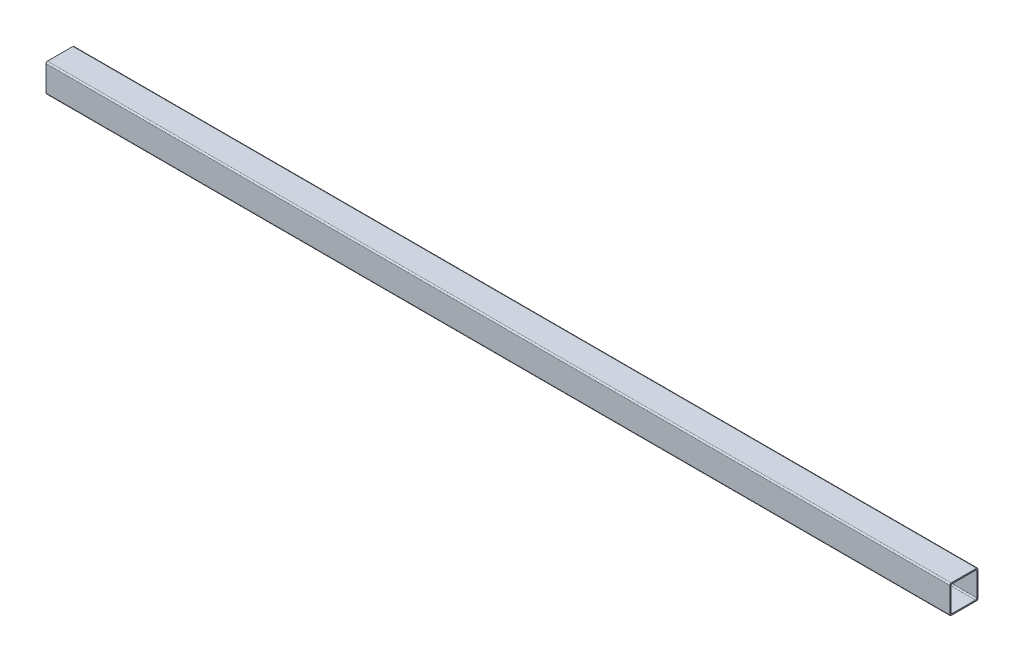
SolidWorks part; units mm, degrees
ref_plane "Front" through (0, 0, 0) normal (0, 0, 1) x (1, 0, 0)
ref_plane "Top" through (0, 0, 0) normal (0, 1, 0) x (1, 0, 0)
ref_plane "Right" through (0, 0, 0) normal (1, 0, 0) x (0, 0, -1)
sketch "Sketch1" plane through (0, 0, 0) normal (1, 0, 0) x (0, 0, -1)
  line L0 (-17.399, 0) -> (-19.05, 0) construction
  line L1 (17.145, -19.05) -> (-17.145, -19.05) construction
  line L2 (19.05, -17.145) -> (19.05, 17.145) construction
  line L3 (17.145, 19.05) -> (-17.145, 19.05) construction
  line L4 (-19.05, -17.145) -> (-19.05, 17.145) construction
  line L5 (19.05, -19.05) -> (-19.05, 19.05) construction
  line L6 (19.05, 19.05) -> (-19.05, -19.05) construction
  line L7 (15.6591, 17.399) -> (-15.6591, 17.399) construction
  line L8 (17.399, 15.6591) -> (17.399, -15.6591) construction
  line L9 (15.6591, -17.399) -> (-15.6591, -17.399) construction
  line L10 (-17.399, 15.6591) -> (-17.399, -15.6591) construction
  line L11 (17.399, 17.399) -> (-17.399, -17.399) construction
  line L12 (17.399, -17.399) -> (-17.399, 17.399) construction
  line L13 (0, -17.399) -> (0, -19.05) construction
  line L14 (17.399, -15.6591) -> (17.399, -19.05) construction
  line L15 (17.399, 0) -> (19.05, 0) construction
  line L16 (17.399, -19.05) -> (19.05, -19.05) construction
  arc A0 (-15.6591, -17.399) -> (-17.399, -15.6591) centre (-15.6591, -15.6591) cw construction
  arc A1 (17.399, -15.6591) -> (15.6591, -17.399) centre (15.6591, -15.6591) cw construction
  arc A2 (15.6591, 17.399) -> (17.399, 15.6591) centre (15.6591, 15.6591) cw construction
  arc A3 (-15.6591, 17.399) -> (-17.399, 15.6591) centre (-15.6591, 15.6591) ccw construction
  arc A4 (17.145, -19.05) -> (19.05, -17.145) centre (17.145, -17.145) ccw construction
  arc A5 (19.05, 17.145) -> (17.145, 19.05) centre (17.145, 17.145) ccw construction
  arc A6 (-17.145, 19.05) -> (-19.05, 17.145) centre (-17.145, 17.145) ccw construction
  arc A7 (-17.145, -19.05) -> (-19.05, -17.145) centre (-17.145, -17.145) cw construction
  point P0 (0, 0)
  point P6 (0, 0)
  dimension "D2" = 1.7399
  dimension "D3" = 1.905
  dimension "Outside Width" = 38.1
  dimension "Ouside Height" = 38.1
  dimension "Inside Height" = 34.798
  dimension "Wall Thickness" = 1.651
sketch "Sketch2" plane through (0, 0, 0) normal (0, 0, 1) x (1, 0, 0)
  line L0 (-914.4, 0) -> (914.4, 0) construction
  point P3 (-877.951, 0)
  point P4 (877.951, 0)
  dimension "Length" = 1828.8
  dimension "D1" = 36.449
  dimension "D2" = 36.449
sketch "Sketch4" plane through (0, 0, 0) normal (1, 0, 0) x (0, 0, -1)
  line L8 (19.05, -17.145) -> (19.05, 17.145)
  line L9 (17.145, 19.05) -> (-17.145, 19.05)
  line L10 (-19.05, -17.145) -> (-19.05, 17.145)
  line L11 (17.145, -19.05) -> (-17.145, -19.05)
  line L12 (17.399, 15.6591) -> (17.399, -15.6591)
  line L13 (15.6591, -17.399) -> (-15.6591, -17.399)
  line L14 (-17.399, 15.6591) -> (-17.399, -15.6591)
  line L15 (15.6591, 17.399) -> (-15.6591, 17.399)
  arc A8 (19.05, 17.145) -> (17.145, 19.05) centre (17.145, 17.145) ccw
  arc A9 (-17.145, 19.05) -> (-19.05, 17.145) centre (-17.145, 17.145) ccw
  arc A10 (-19.05, -17.145) -> (-17.145, -19.05) centre (-17.145, -17.145) ccw
  arc A11 (17.145, -19.05) -> (19.05, -17.145) centre (17.145, -17.145) ccw
  arc A12 (15.6591, -17.399) -> (17.399, -15.6591) centre (15.6591, -15.6591) ccw
  arc A13 (-17.399, -15.6591) -> (-15.6591, -17.399) centre (-15.6591, -15.6591) ccw
  arc A14 (-15.6591, 17.399) -> (-17.399, 15.6591) centre (-15.6591, 15.6591) ccw
  arc A15 (17.399, 15.6591) -> (15.6591, 17.399) centre (15.6591, 15.6591) ccw
extrude "Boss-Extrude1" add sketch "Sketch4" along normal up to vertex (914.4 mm away) and the other way up to vertex (914.4 mm away)
sketch "Sketch5" plane through (0, -19.05, 0) normal (0, -1, 0) x (1, 0, 0)
  line L1 (-914.4, -19.05) -> (-304.8, -19.05)
  line L2 (-914.4, -19.05) -> (-914.4, 19.05)
  line L3 (-914.4, 19.05) -> (-304.8, 19.05)
  line L4 (-304.8, -19.05) -> (-304.8, 19.05)
  line L5 (914.4, 19.05) -> (-914.4, 19.05) construction
  point P4 (0, 0)
  dimension "D1" = 609.6
extrude "Cut-Extrude1" cut sketch "Sketch5" against normal through all
equation "\"D3@Sketch1\"=\"Outside Width@Sketch1\"*.05"
equation "\"D2@Sketch1\" = \"Inside Height@Sketch1\" * .05"
equation "\"D1@Sketch2\"=\"Outside Width@Sketch1\"-\"Wall Thickness@Sketch1\""
equation "\"D2@Sketch2\"=\"D1@Sketch2\""
